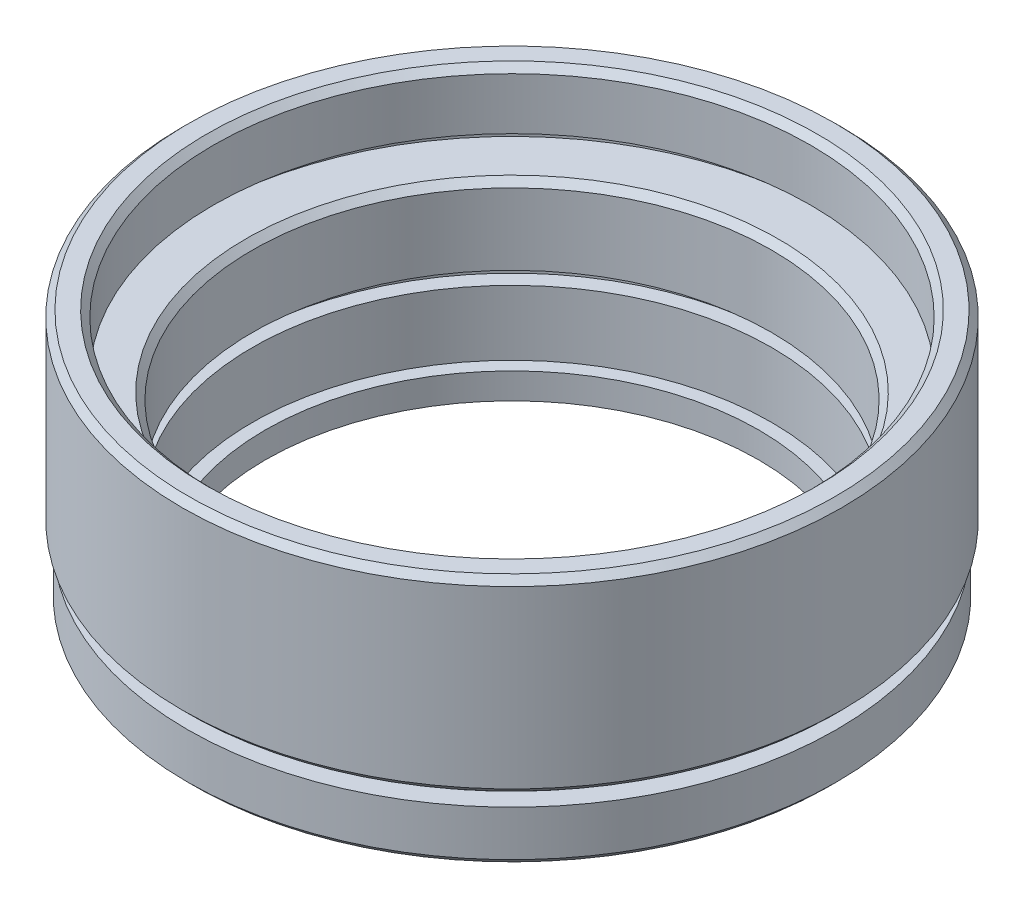
SolidWorks part; units mm, degrees
ref_plane "前视基准面" through (0, 0, 0) normal (0, 0, 1) x (1, 0, 0)
ref_plane "上视基准面" through (0, 0, 0) normal (0, 1, 0) x (1, 0, 0)
ref_plane "右视基准面" through (0, 0, 0) normal (1, 0, 0) x (0, 0, -1)
sketch "草图1" plane through (0, 0, 0) normal (0, 0, 1) x (1, 0, 0)
  line L0 (0, 0) -> (0, 51.3875) construction
  line L1 (19, 0) -> (19, 2)
  line L2 (19, 2) -> (20, 2)
  line L3 (20, 2) -> (20, 7)
  line L4 (20, 7) -> (21.15, 7)
  line L5 (21.15, 7) -> (21.15, 8)
  line L6 (21.15, 8) -> (20, 8)
  line L7 (20, 8) -> (20, 14)
  line L8 (20, 14) -> (24.15, 14)
  line L9 (19, 0) -> (24.5, 0)
  line L10 (24.15, 14) -> (24.15, 15)
  line L11 (24.15, 15) -> (23, 15)
  line L12 (23, 15) -> (23, 19.5)
  line L13 (23, 19.5) -> (24.9, 19.5)
  line L14 (0, 0) -> (5.8539, 0) construction
  line L15 (25, 0.5) -> (25, 4)
  line L16 (25, 4) -> (23.5, 4)
  line L17 (23.5, 4) -> (23.5, 5)
  line L18 (23.5, 5) -> (24.9, 5)
  line L19 (25.4, 5.5) -> (25.4, 19)
  line L20 (24.5, 0) -> (25, 0.5)
  line L21 (24.9, 5) -> (25.4, 5.5)
  line L22 (25.4, 19) -> (24.9, 19.5)
  point P13 (25, 0)
  point P22 (25.4, 5)
  point P24 (25.4, 19.5)
  dimension "D1" = 19
  dimension "D2" = 2
  dimension "D3" = 20
  dimension "D4" = 5
  dimension "D5" = 21.15
  dimension "D6" = 1
  dimension "D7" = 20
  dimension "D8" = 1
  dimension "D9" = 24.15
  dimension "D10" = 5.5
  dimension "D11" = 14.5
  dimension "D12" = 23
  dimension "D13" = 25
  dimension "D14" = 1
  dimension "D15" = 0.5
  dimension "D16" = 23.5
  dimension "D17" = 25.4
  dimension "D18" = 0.5
  dimension "D19" = 45
  dimension "D20" = 45
  dimension "D21" = 0.5
  dimension "D22" = 45
  dimension "D23" = 5
revolve "旋转1" add sketch "草图1" angle 360 about L0
cosmetic thread "装饰螺纹线1" parameters "D2"=48
cosmetic thread "装饰螺纹线2" parameters "D2"=48
cosmetic thread "装饰螺纹线3" parameters "D2"=42
chamfer "倒角1" distance 0.5 angle 45 2 edges at (0, 14, -20) (0, 19.5, -23)
